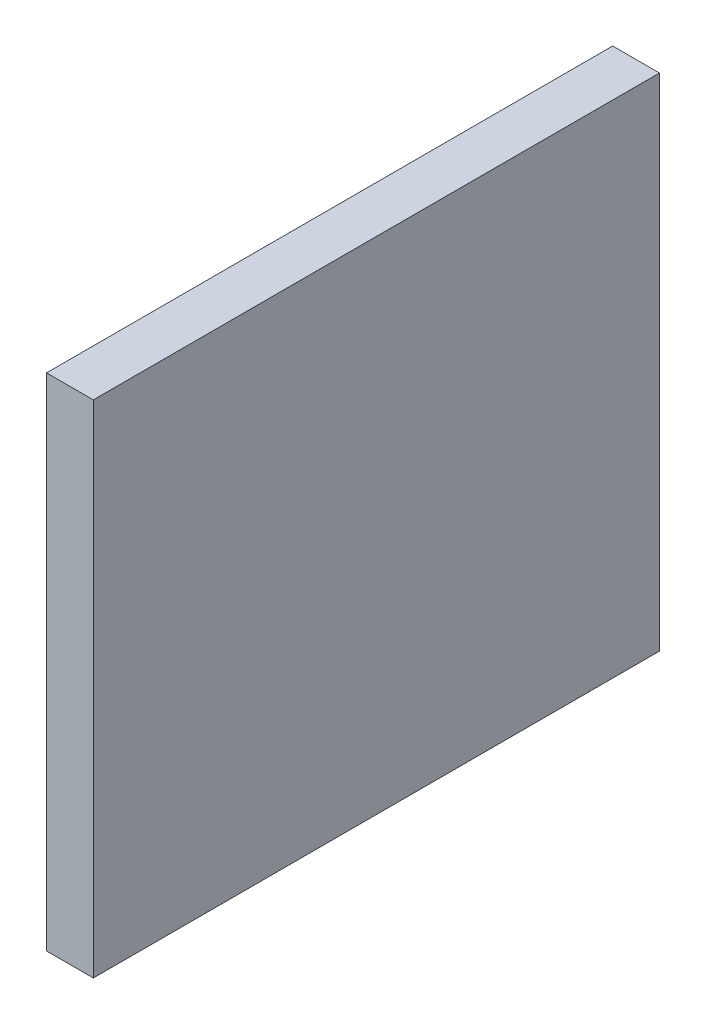
SolidWorks part; units mm, degrees
ref_plane "Front Plane" through (0, 0, 0) normal (0, 0, 1) x (1, 0, 0)
ref_plane "Top Plane" through (0, 0, 0) normal (0, 1, 0) x (1, 0, 0)
ref_plane "Right Plane" through (0, 0, 0) normal (1, 0, 0) x (0, 0, -1)
sketch "Sketch2" plane through (0, 0, -331.8) normal (0, 0, 1) x (1, 0, 0)
  line L0 (-122.1, 0) -> (-127.1, 0)
  line L1 (-122.1, 0) -> (-122.1, -53.5024)
  line L2 (-127.1, 0) -> (-127.1, -53.5024)
  line L3 (-122.1, -53.5024) -> (-127.1, -53.5024)
  line L4 (-249.6, 0) -> (0, 0) construction
  line L7 (-124.6, 0) -> (-124.6, -350.4) construction
  point P8 (-124.6, -53.5024)
  dimension "D1" = 5
extrude "Boss-Extrude1" add sketch "Sketch2" along normal up to surface (60.5 mm away)
